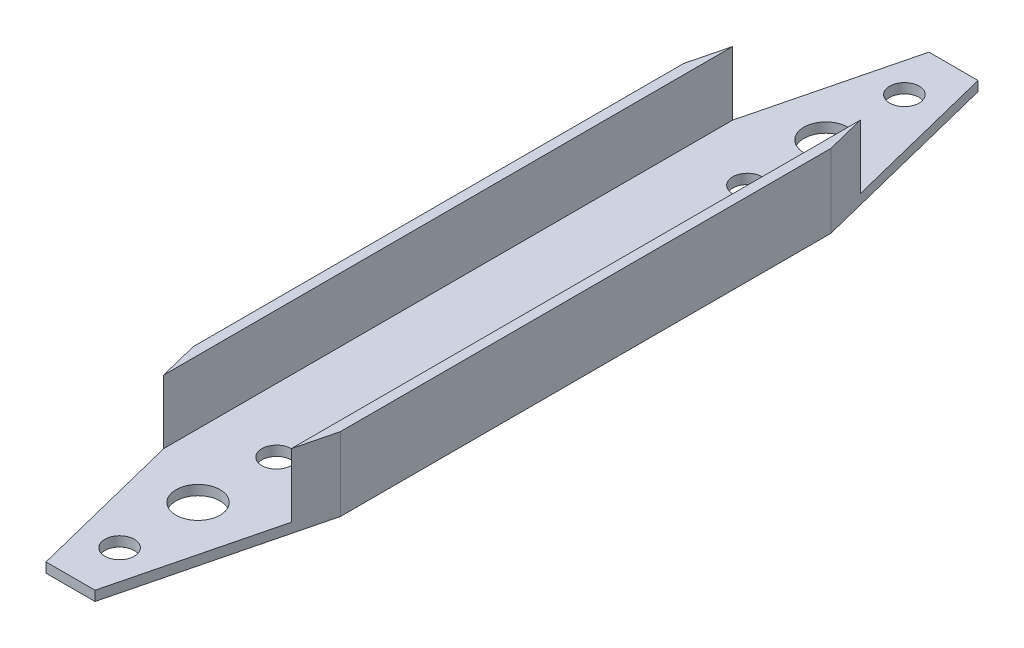
SolidWorks part; units mm, degrees
material "1060 slitina"
ref_plane "Front" through (0, 0, 0) normal (0, 0, 1) x (1, 0, 0)
ref_plane "Top" through (0, 0, 0) normal (0, 1, 0) x (1, 0, 0)
ref_plane "Right" through (0, 0, 0) normal (1, 0, 0) x (0, 0, -1)
sketch "Skica1" plane through (0, 0, 0) normal (0, 0, 1) x (1, 0, 0)
  line L0 (28, 15) -> (30, 15)
  line L1 (0, 0) -> (30, 0)
  line L2 (0, 0) -> (0, 15)
  line L3 (0, 15) -> (2, 15)
  line L4 (30, 0) -> (30, 15)
  line L6 (2, 15) -> (2, 2)
  line L7 (2, 2) -> (28, 2)
  line L8 (28, 15) -> (28, 2)
  dimension "D1" = 30
  dimension "D2" = 15
  dimension "D3" = 2
  dimension "D4" = 2
  dimension "D5" = 2
extrude "Přidat vysunutím1" add sketch "Skica1" along normal blind 180
sketch "Skica2" plane through (0, 2, 0) normal (0, 1, 0) x (1, 0, 0)
  line L0 (15, -180) -> (15, 0) construction
  line L1 (28, -180) -> (2, -180) construction
  line L2 (28, 0) -> (2, 0) construction
  line L3 (15.71, -154) -> (50015.71, -154) construction
  line L5 (2, -90) -> (50002, -90) construction
  line L6 (2, -180) -> (2, 0) construction
  line L7 (28, -180) -> (28, 0) construction
  circle A0 centre (15, -170) radius 3
  circle A1 centre (15, -154) radius 4.5
  circle A2 centre (15, -138) radius 3
  circle A3 centre (15, -42) radius 3
  circle A4 centre (15, -26) radius 4.5
  circle A5 centre (15, -10) radius 3
  point P20 (2, -90)
  point P23 (28, -90)
  dimension "D1" = 26
  dimension "D2" = 9
  dimension "D3" = 6
  dimension "D4" = 16
extrude "Odebrat vysunutím1" cut sketch "Skica2" against normal up to next
sketch "Skica3" plane through (0, 0, 0) normal (0, -1, 0) x (1, 0, 0)
  line L0 (15, 180) -> (15, -49820) construction
  line L3 (0, 0) -> (30, 0) construction
  line L4 (0, 90) -> (50000, 90) construction
  line L5 (30, 180) -> (30, 0) construction
  line L6 (0, 180) -> (0, 0) construction
  line L7 (30, 180) -> (20, 180)
  line L8 (30, 140) -> (30, 180)
  line L9 (20, 180) -> (30, 140)
  line L10 (0, 180) -> (30, 180) construction
  line L11 (0, 0) -> (10, 0)
  line L12 (0, 40) -> (0, 0)
  line L13 (10, 180) -> (0, 140)
  line L14 (0, 140) -> (0, 180)
  line L15 (0, 180) -> (10, 180)
  line L16 (10, 0) -> (0, 40)
  line L17 (20, 0) -> (30, 40)
  line L18 (30, 40) -> (30, 0)
  line L19 (30, 0) -> (20, 0)
  point P2 (15, 180)
  point P5 (15, 0)
  point P9 (0, 90)
  point P15 (30, 90)
  dimension "D6" = 10
  dimension "D7" = 40
extrude "Odebrat vysunutím2" cut sketch "Skica3" against normal up to surface (15 mm away) up to face at (29, 15, 90)
fillet "Zaoblit1" [suppressed] radius 3
